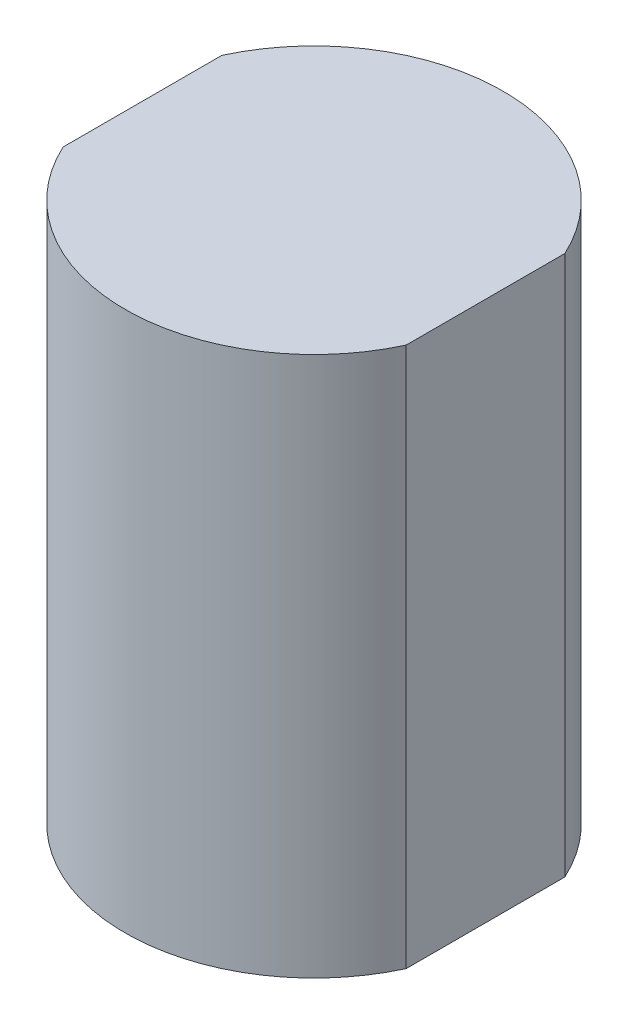
SolidWorks part; units mm, degrees
ref_plane "Front Plane" through (0, 0, 0) normal (0, 0, 1) x (1, 0, 0)
ref_plane "Top Plane" through (0, 0, 0) normal (0, 1, 0) x (1, 0, 0)
ref_plane "Right Plane" through (0, 0, 0) normal (1, 0, 0) x (0, 0, -1)
sketch "Sketch1" plane through (0, 0, 0) normal (0, 1, 0) x (1, 0, 0)
  line L0 (-3.1763, -1.47) -> (-3.1763, 1.47)
  line L1 (3.1763, -1.47) -> (3.1763, 1.47)
  circle A0 centre (0, 0) radius 3.5
  point P7 (0, 0)
  point P8 (0, 0)
extrude "Boss-Extrude1" add sketch "Sketch1" along normal blind 10 contours L1 A0 L0
